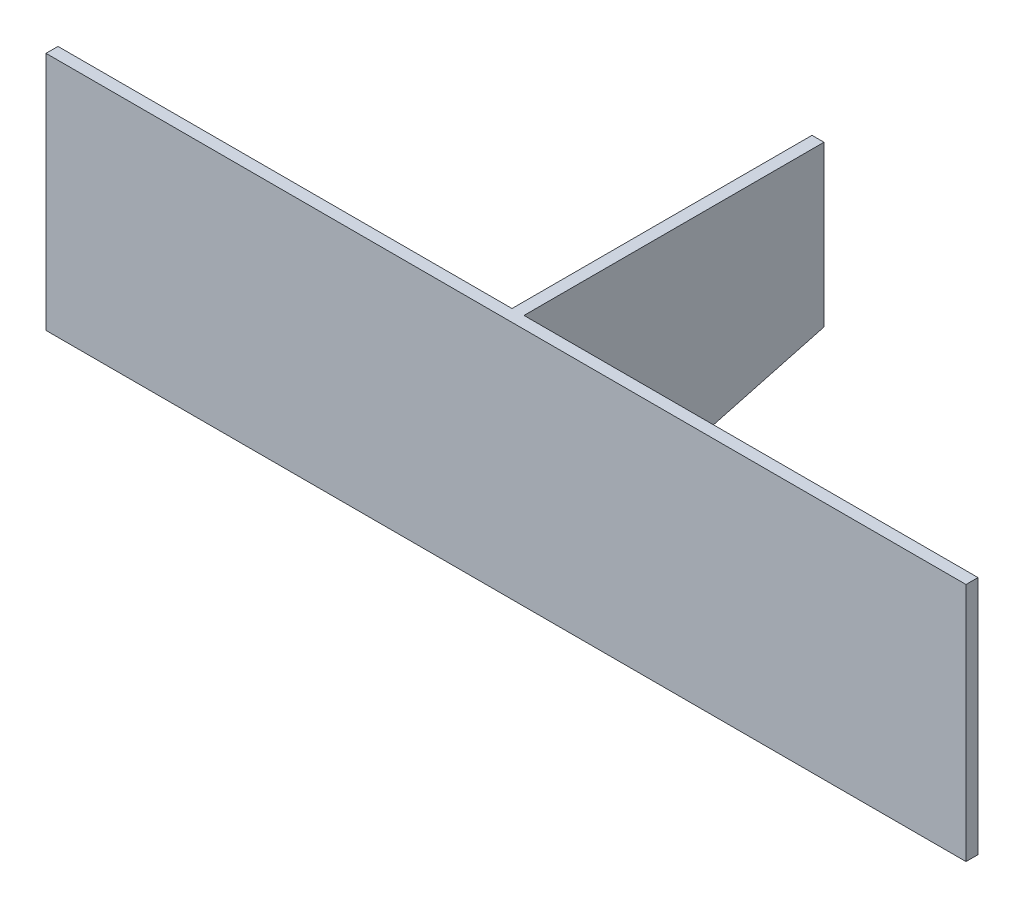
SolidWorks part; units mm, degrees
material "Balsa"
ref_plane "Front Plane" through (0, 0, 0) normal (0, 0, 1) x (1, 0, 0)
ref_plane "Top Plane" through (0, 0, 0) normal (0, 1, 0) x (1, 0, 0)
ref_plane "Right Plane" through (0, 0, 0) normal (1, 0, 0) x (0, 0, -1)
sketch "Sketch1" plane through (0, 0, 0) normal (0, 0, 1) x (1, 0, 0)
  line L1 (-115, 30) -> (115, 30)
  line L2 (-115, 30) -> (-115, -30)
  line L3 (-115, -30) -> (115, -30)
  line L4 (115, 30) -> (115, -30)
  line L5 (-115, 30) -> (115, -30) construction
  line L6 (-115, -30) -> (115, 30) construction
  point P0 (0, 0)
  dimension "D1" = 230
  dimension "D2" = 60
extrude "Boss-Extrude1" add sketch "Sketch1" along normal blind 3
sketch "Sketch2" plane through (0, 0, 0) normal (0, 0, -1) x (-1, 0, 0)
  line L0 (-115, 0) -> (115, 0) construction
  line L1 (-115, -30) -> (-115, 30) construction
  line L2 (115, 30) -> (115, -30) construction
  line L3 (115, -30) -> (-115, -30) construction
  line L4 (-1.5, 30) -> (1.5, 30)
  line L5 (-1.5, 30) -> (-1.5, -30)
  line L6 (-1.5, -30) -> (1.5, -30)
  line L7 (1.5, 30) -> (1.5, -30)
  line L8 (-1.5, 30) -> (1.5, -30) construction
  line L9 (-1.5, -30) -> (1.5, 30) construction
  point P6 (0, 0)
  dimension "D1" = 3
extrude "Boss-Extrude2" add sketch "Sketch2" along normal blind 75
sketch "Sketch3" plane through (1.5, 0, 0) normal (1, 0, 0) x (0, 0, -1)
  line L2 (75, 30) -> (75, -30) construction
  line L3 (75, -10) -> (0, -30)
  line L5 (75, -10) -> (75, -30)
  line L6 (75, -30) -> (0, -30)
extrude "Cut-Extrude1" cut sketch "Sketch3" against normal blind 75
